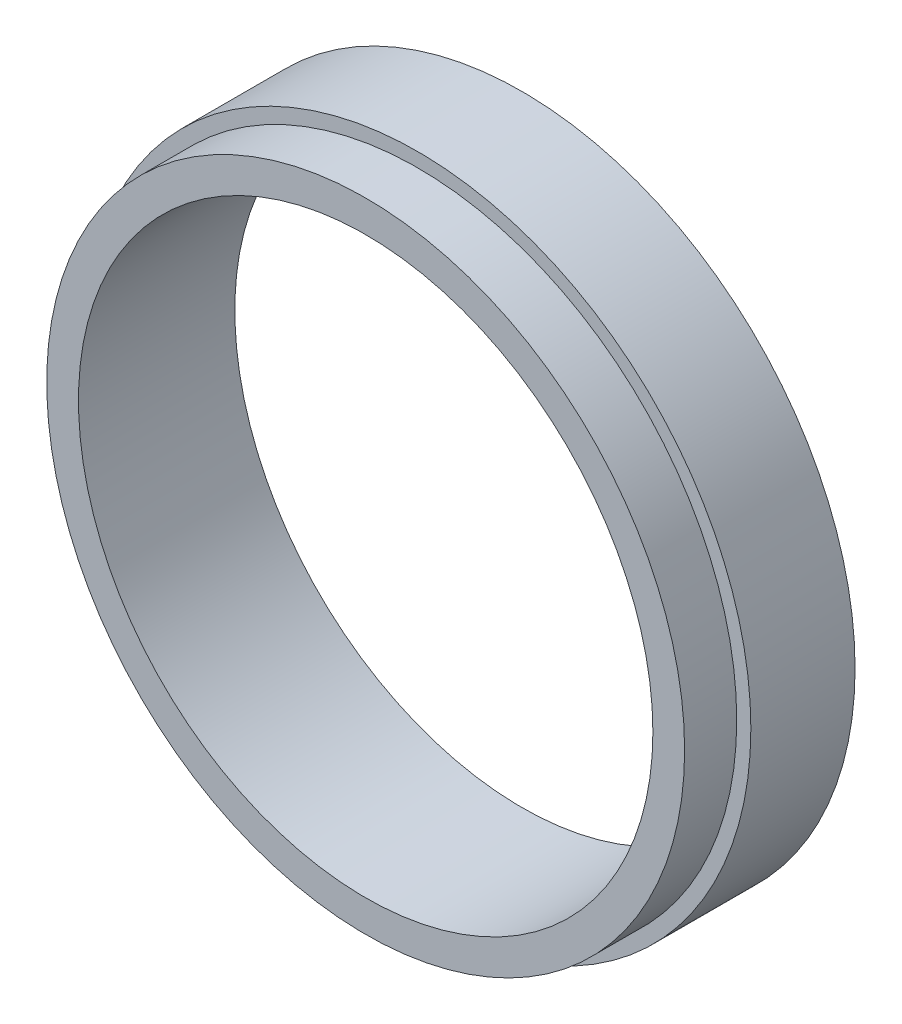
SolidWorks part; units mm, degrees
material "6061 Alloy"
ref_plane "Front Plane" through (0, 0, 0) normal (0, 0, 1) x (1, 0, 0)
ref_plane "Top Plane" through (0, 0, 0) normal (0, 1, 0) x (1, 0, 0)
ref_plane "Right Plane" through (0, 0, 0) normal (1, 0, 0) x (0, 0, -1)
sketch "Sketch1" plane through (0, 0, 0) normal (1, 0, 0) x (0, 0, -1)
  line L0 (-1000, 0) -> (49000, 0) construction
  line L1 (0, 17.5) -> (9.525, 17.5)
  line L2 (9.525, 17.5) -> (9.525, 20.294)
  line L3 (9.525, 20.294) -> (3.175, 20.294)
  line L4 (3.175, 20.294) -> (3.175, 19.4337)
  line L5 (3.175, 19.4337) -> (0, 19.4337)
  line L6 (0, 19.4337) -> (0, 17.5)
  dimension "D1" = 35
  dimension "D2" = 38.8674
  dimension "D3" = 3.175
  dimension "D4" = 2.794
  dimension "D5" = 6.35
revolve "Revolve1" add sketch "Sketch1" angle 360 about L0
